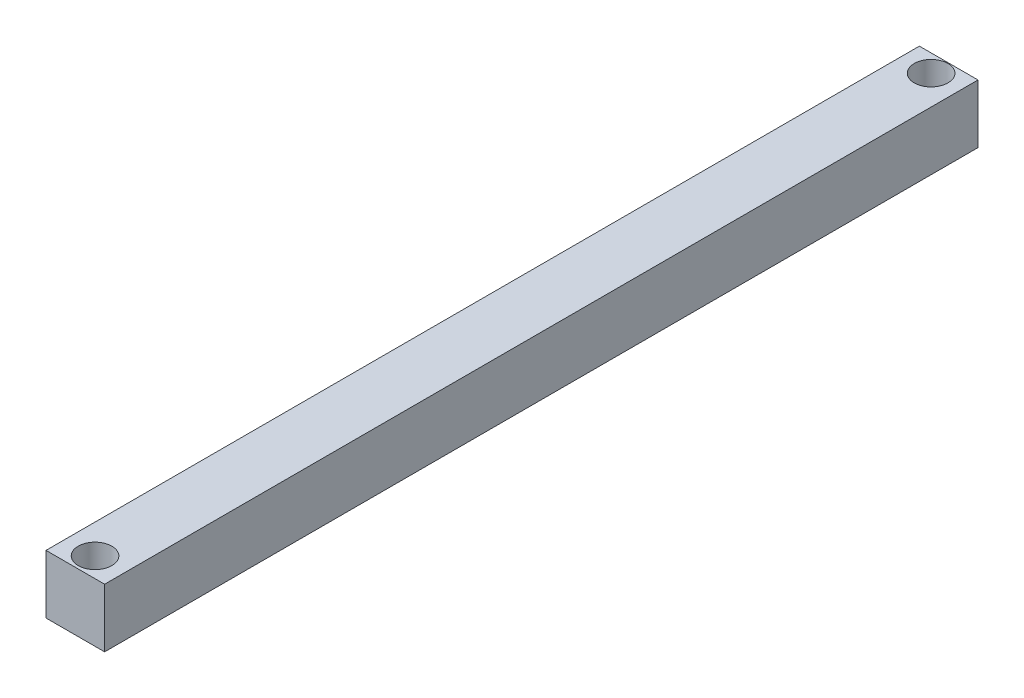
SolidWorks part; units mm, degrees
ref_plane "Front Plane" through (0, 0, 0) normal (0, 0, 1) x (1, 0, 0)
ref_plane "Top Plane" through (0, 0, 0) normal (0, 1, 0) x (1, 0, 0)
ref_plane "Right Plane" through (0, 0, 0) normal (1, 0, 0) x (0, 0, -1)
sketch "Sketch1" plane through (0, 0, 0) normal (0, 1, 0) x (1, 0, 0)
  line L1 (-10, 149) -> (10, 149)
  line L2 (-10, 149) -> (-10, -149)
  line L3 (-10, -149) -> (10, -149)
  line L4 (10, 149) -> (10, -149)
  line L5 (-10, 149) -> (10, -149) construction
  line L6 (-10, -149) -> (10, 149) construction
  point P0 (0, 0)
  dimension "D1" = 20
  dimension "D2" = 298
extrude "Boss-Extrude1" add sketch "Sketch1" along normal blind 20
sketch "Sketch3" plane through (0, 20, 0) normal (0, 1, 0) x (1, 0, 0)
  line L0 (10, 149) -> (-10, 149) construction
  line L1 (10, -149) -> (10, 149) construction
  line L2 (0, 143) -> (0, -142.27) construction
  circle A0 centre (0, 143) radius 5.75
  circle A1 centre (0, -142.27) radius 5.75
  dimension "D1" = 11.5
  dimension "D5" = 11.5
  dimension "D2" = 6
  dimension "D3" = 10
  dimension "D4" = 285.27
extrude "Cut-Extrude1" cut sketch "Sketch3" against normal through all
